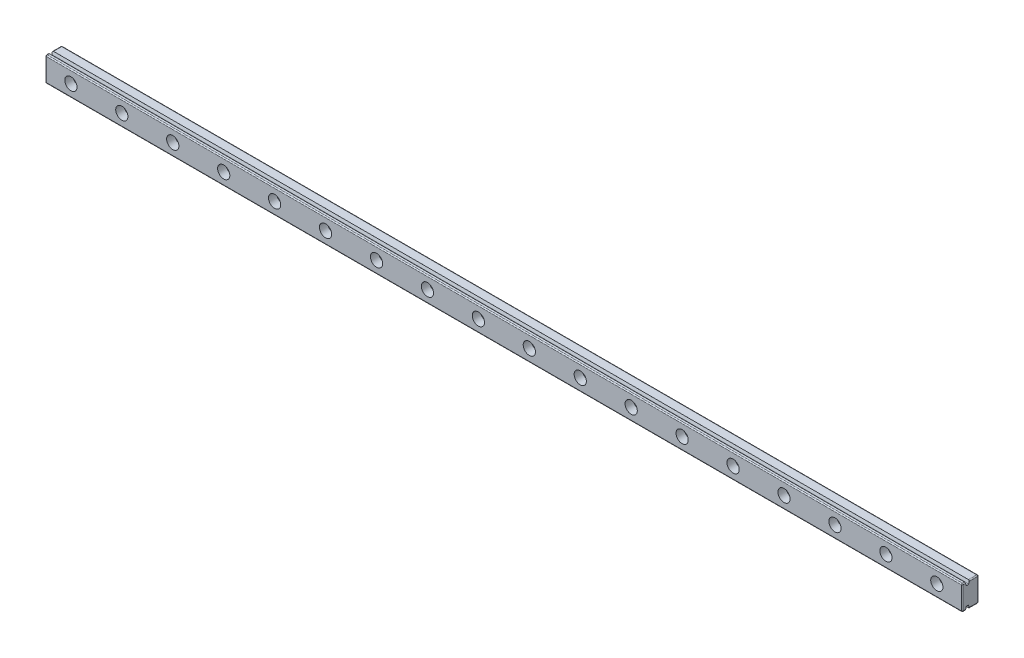
SolidWorks part; units mm, degrees
ref_plane "Front Plane" through (0, 0, 0) normal (0, 0, 1) x (1, 0, 0)
ref_plane "Top Plane" through (0, 0, 0) normal (0, 1, 0) x (1, 0, 0)
ref_plane "Right Plane" through (0, 0, 0) normal (1, 0, 0) x (0, 0, -1)
sketch "Sketch1" plane through (0, 0, 0) normal (1, 0, 0) x (0, 0, -1)
  line L0 (-0.5, 6) -> (4, 6)
  line L1 (-4, 6) -> (-2.5, 6)
  line L2 (-4, 6) -> (-4, -6)
  line L3 (-4, -6) -> (-2.5, -6)
  line L4 (4, 6) -> (4, -6)
  line L5 (-4, 6) -> (4, -6) construction
  line L6 (-4, -6) -> (4, 6) construction
  line L8 (-2.5, 6) -> (-2.5, 4.25)
  line L9 (-2.5, 4.25) -> (-0.5, 4.25)
  line L10 (-0.5, 6) -> (-0.5, 4.25)
  line L12 (-2.5, -6) -> (-2.5, -4.25)
  line L13 (-2.5, -4.25) -> (-0.5, -4.25)
  line L14 (-0.5, -6) -> (-0.5, -4.25)
  line L15 (-0.5, -6) -> (4, -6)
  point P0 (0, 0)
  dimension "D1" = 12
  dimension "D2" = 8
  dimension "D3" = 2
  dimension "D4" = 2
  dimension "D5" = 1.5
  dimension "D6" = 1.5
  dimension "D7" = 8.5
  dimension "D8" = 4.25
extrude "Boss-Extrude1" add sketch "Sketch1" along normal blind 450
sketch "Sketch2" plane through (0, 0, 4) normal (0, 0, 1) x (1, 0, 0)
  line L0 (0, 6) -> (0, -6) construction
  circle A0 centre (12.5, 0) radius 1.75
  circle A1 centre (37.5, 0) radius 1.75
  circle A2 centre (62.5, 0) radius 1.75
  circle A3 centre (87.5, 0) radius 1.75
  circle A4 centre (112.5, 0) radius 1.75
  circle A5 centre (137.5, 0) radius 1.75
  circle A6 centre (162.5, 0) radius 1.75
  circle A7 centre (187.5, 0) radius 1.75
  circle A8 centre (212.5, 0) radius 1.75
  circle A9 centre (237.5, 0) radius 1.75
  circle A10 centre (262.5, 0) radius 1.75
  circle A11 centre (287.5, 0) radius 1.75
  circle A12 centre (312.5, 0) radius 1.75
  circle A13 centre (337.5, 0) radius 1.75
  circle A14 centre (362.5, 0) radius 1.75
  circle A15 centre (387.5, 0) radius 1.75
  circle A16 centre (412.5, 0) radius 1.75
  circle A17 centre (437.5, 0) radius 1.75
  dimension "D1" = 3.5
  dimension "D2" = 12.5
  dimension "D3" = 18
extrude "Cut-Extrude1" cut sketch "Sketch2" against normal blind 10
sketch "Sketch3" plane through (0, 0, 4) normal (0, 0, 1) x (1, 0, 0)
  circle A0 centre (12.5, 0) radius 3
  circle A1 centre (37.5, 0) radius 3
  circle A2 centre (62.5, 0) radius 3
  circle A3 centre (87.5, 0) radius 3
  circle A4 centre (112.5, 0) radius 3
  circle A5 centre (137.5, 0) radius 3
  circle A6 centre (162.5, 0) radius 3
  circle A7 centre (187.5, 0) radius 3
  circle A8 centre (212.5, 0) radius 3
  circle A9 centre (237.5, 0) radius 3
  circle A10 centre (262.5, 0) radius 3
  circle A11 centre (287.5, 0) radius 3
  circle A12 centre (312.5, 0) radius 3
  circle A13 centre (337.5, 0) radius 3
  circle A14 centre (362.5, 0) radius 3
  circle A15 centre (387.5, 0) radius 3
  circle A16 centre (412.5, 0) radius 3
  circle A17 centre (437.5, 0) radius 3
  dimension "D1" = 6
  dimension "D2" = 18
extrude "Cut-Extrude2" cut sketch "Sketch3" against normal blind 4
chamfer "Chamfer1" distance 0.5 angle 74 4 edges at (225, -4.25, 2.5) (225, -4.25, 0.5) (225, 4.25, 2.5) (225, 4.25, 0.5)
fillet "Fillet1" radius 0.5 20 edges at (450, -6, -1.75) (450, 0, -4) (450, 6, -1.75) (450, 6, 3.25) (450, 0, 4) (450, -6, 3.25) (0, -6, 3.25) (0, -6, -1.75) (0, 0, -4) (0, 6, -1.75) (0, 6, 3.25) (0, 0, 4) (225, -4.25, 1) (225, -4.25, 2) (225, 4.25, 2) (225, 4.25, 1) (225, -6, 4) (225, 6, 4) (225, -6, -4) (225, 6, -4)
